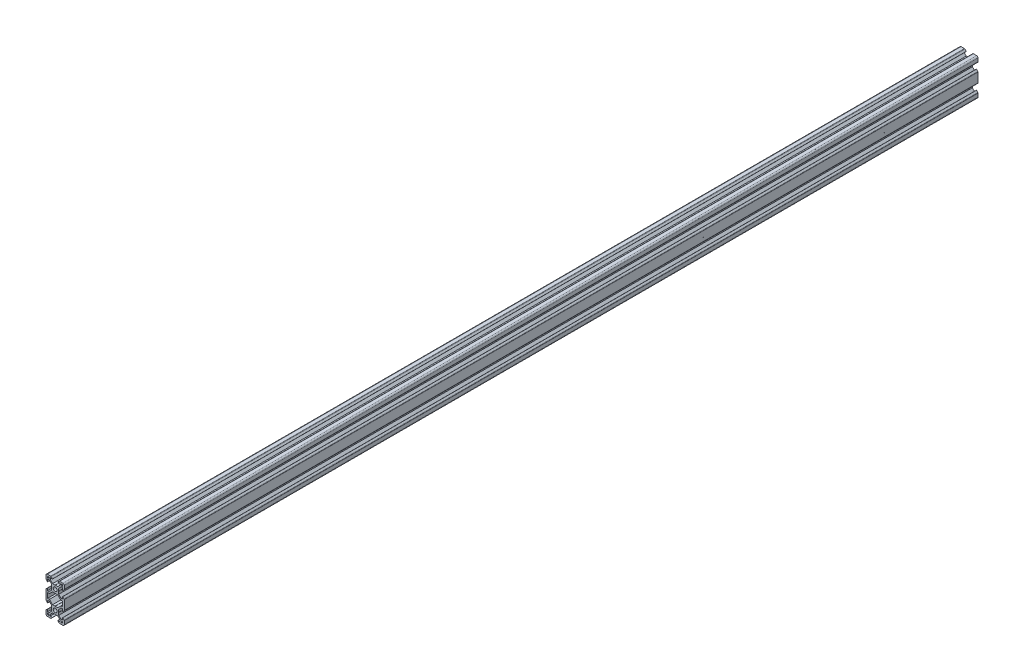
SolidWorks part; units mm, degrees
ref_plane "Front Plane" through (0, 0, 0) normal (0, 0, 1) x (1, 0, 0)
ref_plane "Top Plane" through (0, 0, 0) normal (0, 1, 0) x (1, 0, 0)
ref_plane "Right Plane" through (0, 0, 0) normal (1, 0, 0) x (0, 0, -1)
sketch "Sketch1" plane through (0, 0, 0) normal (0, 0, 1) x (1, 0, 0)
  line L0 (-8.2, 2.8875) -> (-8.2, 5.4975)
  line L3 (-4.9072, 9.9975) -> (-8.5, 9.9975)
  line L4 (-10, 4.9047) -> (-10, 8.4975)
  line L5 (-2.1, 0) -> (-3.8, 0) construction
  line L6 (0, 3.8) -> (0, 0) construction
  line L7 (-0.1, 3.9) -> (-2.8404, 3.9)
  line L8 (-3.9, 0.1) -> (-3.9, 2.8383)
  line L9 (-2.89, 8.1975) -> (-5.5, 8.1975)
  line L10 (-6.57, 8.1975) -> (-6.57, 7.6575)
  line L11 (-8.2, 6.5675) -> (-7.66, 6.5675)
  line L12 (-5.5, 8.1975) -> (-5.5, 6.5588)
  line L13 (-6.56, 5.4975) -> (-8.2, 5.4975)
  line L14 (-8.2, 8.1975) -> (-1.4852, 1.4847) construction
  line L15 (-6.56, 5.4975) -> (-3.9, 2.8383)
  line L16 (-5.5, 6.5588) -> (-2.8404, 3.9)
  line L17 (-7.66, 6.5675) -> (-6.57, 7.6575)
  line L18 (-8.7302, 7.6671) -> (-0.5302, -0.5304) construction
  line L19 (-7.6698, 8.7279) -> (0.5302, 0.5304) construction
  line L20 (-8.2, 8.1975) -> (0, 0) construction
  line L21 (-8.2, 6.5675) -> (-8.2, 8.1975)
  line L22 (-8.2, -0.0025) -> (-8.2, 8.1975) construction
  line L23 (-6.57, 8.1975) -> (-8.2, 8.1975)
  line L24 (0, 8.1975) -> (-8.2, 8.1975) construction
  line L25 (-10, -0.0025) -> (-10, 9.9975) construction
  line L26 (0, 9.9975) -> (-10, 9.9975) construction
  line L27 (-2.89, 8.3075) -> (-2.89, 8.1975)
  line L29 (-8.31, 2.8875) -> (-8.2, 2.8875)
  line L30 (-4.3486, 9.7661) -> (-2.89, 8.3075)
  line L31 (-8.31, 2.8875) -> (-9.7686, 4.3461)
  line L34 (-0.1, 3.9) -> (0, 3.8)
  line L35 (-3.9, 0.1) -> (-3.8, 0)
  line L36 (-8.2, -7.2996) -> (-6.24, -7.2996)
  line L37 (0, 0) -> (0, -10) construction
  line L38 (-0.1, -3.9) -> (-2.8404, -3.9)
  line L39 (-3.8, 0) -> (-3.9, -0.1)
  line L40 (-3.9, -0.1) -> (-3.9, -2.84)
  line L41 (-2.8404, -3.9) -> (-6.24, -7.2996)
  line L42 (-3.9, -2.84) -> (-6.56, -5.5)
  line L43 (-8.2, -2.89) -> (-8.2, -5.5)
  line L44 (-6.56, 5.4975) -> (-6.56, -5.5) construction
  line L45 (-6.56, -5.5) -> (-8.2, -5.5)
  line L46 (-0.1, -3.9) -> (0, -3.8)
  line L48 (-8.2, -2.89) -> (-8.31, -2.89)
  line L49 (-8.31, -2.89) -> (-9.7657, -4.3457)
  line L52 (-10, -10) -> (0, -10) construction
  line L53 (-8.2, -7.2996) -> (-8.2, -10)
  line L61 (-10, -4.9114) -> (-10, -10)
  arc A1 (-10, 8.4975) -> (-8.5, 9.9975) centre (-8.5, 8.4975) cw
  arc A2 (-9.7686, 4.3461) -> (-10, 4.9047) centre (-9.21, 4.9047) cw
  arc A3 (-4.3486, 9.7661) -> (-4.9072, 9.9975) centre (-4.9072, 9.2075) ccw
  arc A4 (-9.7657, -4.3457) -> (-10, -4.9114) centre (-9.2, -4.9114) ccw
  arc A6 (0, 2.1) -> (0, -2.1) centre (0, 0) ccw
  point P29 (-10, 9.9975)
  point P39 (-10, 4.5775)
  point P42 (-4.58, 9.9975)
  point P48 (-10, -4.58)
  dimension "D15" = 1.5
  dimension "D22" = 0.79
  dimension "D30" = 1.96
  dimension "D31" = 2.1
  dimension "D39" = 0.8
  dimension "D4" = 1.8
  dimension "D5" = 3.43
  dimension "D6" = 3.43
  dimension "D7" = 0.54
  dimension "D8" = 0.54
  dimension "D9" = 1.07
  dimension "D10" = 1.07
  dimension "D11" = 3.9
  dimension "D12" = 3.9
  dimension "D16" = 7.11
  dimension "D17" = 0.11
  dimension "D18" = 1.69
  dimension "D19" = 0.11
  dimension "D20" = 7.11
  dimension "D21" = 1.69
  dimension "D23" = 10
  dimension "D24" = 0.1
  dimension "D25" = 45
  dimension "D26" = 0.1
  dimension "D27" = 45
  dimension "D28" = 1.64
  dimension "D29" = 10
  dimension "D32" = 3.9
  dimension "D33" = 45
  dimension "D34" = 2.74
  dimension "D35" = 45
  dimension "D37" = 2.61
  dimension "D38" = 90
  dimension "D40" = 0.1
  dimension "D41" = 45
  dimension "D13" = 0.75
  dimension "D14" = 0.75
sketch "Sketch2" plane through (0, 0, 0) normal (0, 0, 1) x (1, 0, 0)
  line L0 (-0.1, 3.9) -> (0, 3.8) construction
  line L1 (-0.1, 3.9) -> (-2.8404, 3.9) construction
  line L2 (-5.5, 6.5588) -> (-2.8404, 3.9) construction
  line L3 (-5.5, 8.1975) -> (-5.5, 6.5588) construction
  line L4 (-2.89, 8.1975) -> (-5.5, 8.1975) construction
  line L5 (-7.66, 6.5675) -> (-6.57, 7.6575)
  line L6 (-6.57, 7.6575) -> (-6.57, 8.1975)
  line L7 (-6.57, 8.1975) -> (-8.2, 8.1975)
  line L8 (-8.2, 8.1975) -> (-8.2, 6.5675)
  line L9 (-8.2, 6.5675) -> (-7.66, 6.5675)
  line L10 (-7.66, 6.5675) -> (-6.57, 7.6575)
  line L11 (-6.57, 7.6575) -> (-6.57, 8.1975)
  line L12 (-6.57, 8.1975) -> (-8.2, 8.1975)
  line L13 (-8.2, 8.1975) -> (-8.2, 6.5675)
  line L14 (-8.2, 6.5675) -> (-7.66, 6.5675)
  line L15 (-2.89, 8.3075) -> (-2.89, 8.1975) construction
  line L16 (-4.3486, 9.7661) -> (-2.89, 8.3075) construction
  line L17 (-4.9072, 9.9975) -> (-8.5, 9.9975) construction
  line L18 (-10, 4.9047) -> (-10, 8.4975) construction
  line L19 (-8.31, 2.8875) -> (-9.7686, 4.3461) construction
  line L20 (-8.31, 2.8875) -> (-8.2, 2.8875) construction
  line L21 (-8.2, 2.8875) -> (-8.2, 5.4975) construction
  line L22 (-6.56, 5.4975) -> (-8.2, 5.4975) construction
  line L23 (-6.56, 5.4975) -> (-3.9, 2.8383) construction
  line L24 (-3.9, 0.1) -> (-3.9, 2.8383) construction
  line L25 (-3.9, 0.1) -> (-3.8, 0) construction
  line L26 (-3.8, 0) -> (-3.9, -0.1) construction
  line L27 (-3.9, -0.1) -> (-3.9, -2.84) construction
  line L28 (-3.9, -2.84) -> (-6.56, -5.5) construction
  line L29 (-6.56, -5.5) -> (-8.2, -5.5) construction
  line L30 (-8.2, -2.89) -> (-8.2, -5.5) construction
  line L31 (-8.2, -2.89) -> (-8.31, -2.89) construction
  line L32 (-8.31, -2.89) -> (-9.7657, -4.3457) construction
  line L33 (-10, -4.9114) -> (-10, -10) construction
  line L34 (-0.1, -3.9) -> (0, -3.8) construction
  line L35 (-0.1, -3.9) -> (-2.8404, -3.9) construction
  line L36 (-2.8404, -3.9) -> (-6.24, -7.2996) construction
  line L37 (-8.2, -7.2996) -> (-6.24, -7.2996) construction
  line L38 (-8.2, -7.2996) -> (-8.2, -10) construction
  line L39 (-0.1, 3.9) -> (0, 3.8)
  line L40 (-0.1, 3.9) -> (-2.8404, 3.9)
  line L41 (-5.5, 6.5588) -> (-2.8404, 3.9)
  line L42 (-5.5, 8.1975) -> (-5.5, 6.5588)
  line L43 (-2.89, 8.1975) -> (-5.5, 8.1975)
  line L44 (-2.89, 8.3075) -> (-2.89, 8.1975)
  line L45 (-4.3486, 9.7661) -> (-2.89, 8.3075)
  line L46 (-4.9072, 9.9975) -> (-8.5, 9.9975)
  line L47 (-10, 4.9047) -> (-10, 8.4975)
  line L48 (-8.31, 2.8875) -> (-9.7686, 4.3461)
  line L49 (-8.31, 2.8875) -> (-8.2, 2.8875)
  line L50 (-8.2, 2.8875) -> (-8.2, 5.4975)
  line L51 (-6.56, 5.4975) -> (-8.2, 5.4975)
  line L52 (-6.56, 5.4975) -> (-3.9, 2.8383)
  line L53 (-3.9, 0.1) -> (-3.9, 2.8383)
  line L54 (-3.9, 0.1) -> (-3.8, 0)
  line L55 (-3.8, 0) -> (-3.9, -0.1)
  line L56 (-3.9, -0.1) -> (-3.9, -2.84)
  line L57 (-3.9, -2.84) -> (-6.56, -5.5)
  line L58 (-6.56, -5.5) -> (-8.2, -5.5)
  line L59 (-8.2, -2.89) -> (-8.2, -5.5)
  line L60 (-8.2, -2.89) -> (-8.31, -2.89)
  line L61 (-8.31, -2.89) -> (-9.7657, -4.3457)
  line L62 (-10, -4.9114) -> (-10, -15.0886)
  line L63 (-0.1, -3.9) -> (0, -3.8)
  line L64 (-0.1, -3.9) -> (-2.8404, -3.9)
  line L65 (-2.8404, -3.9) -> (-6.24, -7.2996)
  line L66 (-8.2, -7.2996) -> (-6.24, -7.2996)
  line L67 (-8.2, -7.2996) -> (-8.2, -12.7004)
  line L68 (0, 0) -> (0, -10) construction
  line L69 (-10, -10) -> (0, -10) construction
  line L70 (0, 0) -> (0, -20) construction
  line L71 (-10, -10) -> (10, -10) construction
  line L72 (8.2, -7.2996) -> (8.2, -12.7004)
  line L73 (8.2, -7.2996) -> (6.24, -7.2996)
  line L74 (2.8404, -3.9) -> (6.24, -7.2996)
  line L75 (0.1, -3.9) -> (2.8404, -3.9)
  line L76 (0.1, -3.9) -> (0, -3.8)
  line L77 (10, -4.9114) -> (10, -15.0886)
  line L78 (8.31, -2.89) -> (9.7657, -4.3457)
  line L79 (8.2, -2.89) -> (8.31, -2.89)
  line L80 (8.2, -2.89) -> (8.2, -5.5)
  line L81 (6.56, -5.5) -> (8.2, -5.5)
  line L82 (3.9, -2.84) -> (6.56, -5.5)
  line L83 (3.9, -0.1) -> (3.9, -2.84)
  line L84 (3.8, 0) -> (3.9, -0.1)
  line L85 (3.9, 0.1) -> (3.8, 0)
  line L86 (3.9, 0.1) -> (3.9, 2.8383)
  line L87 (6.56, 5.4975) -> (3.9, 2.8383)
  line L88 (6.56, 5.4975) -> (8.2, 5.4975)
  line L89 (8.2, 2.8875) -> (8.2, 5.4975)
  line L90 (8.31, 2.8875) -> (8.2, 2.8875)
  line L91 (8.31, 2.8875) -> (9.7686, 4.3461)
  line L92 (10, 4.9047) -> (10, 8.4975)
  line L93 (4.9072, 9.9975) -> (8.5, 9.9975)
  line L94 (4.3486, 9.7661) -> (2.89, 8.3075)
  line L95 (2.89, 8.3075) -> (2.89, 8.1975)
  line L96 (2.89, 8.1975) -> (5.5, 8.1975)
  line L97 (5.5, 8.1975) -> (5.5, 6.5588)
  line L98 (5.5, 6.5588) -> (2.8404, 3.9)
  line L99 (0.1, 3.9) -> (2.8404, 3.9)
  line L100 (0.1, 3.9) -> (0, 3.8)
  line L101 (8.2, 6.5675) -> (7.66, 6.5675)
  line L102 (8.2, 8.1975) -> (8.2, 6.5675)
  line L103 (6.57, 8.1975) -> (8.2, 8.1975)
  line L104 (6.57, 7.6575) -> (6.57, 8.1975)
  line L105 (7.66, 6.5675) -> (6.57, 7.6575)
  line L106 (7.66, -26.5675) -> (6.57, -27.6575)
  line L107 (6.57, -27.6575) -> (6.57, -28.1975)
  line L108 (6.57, -28.1975) -> (8.2, -28.1975)
  line L109 (8.2, -28.1975) -> (8.2, -26.5675)
  line L110 (8.2, -26.5675) -> (7.66, -26.5675)
  line L111 (0.1, -23.9) -> (0, -23.8)
  line L112 (0.1, -23.9) -> (2.8404, -23.9)
  line L113 (5.5, -26.5588) -> (2.8404, -23.9)
  line L114 (5.5, -28.1975) -> (5.5, -26.5588)
  line L115 (2.89, -28.1975) -> (5.5, -28.1975)
  line L116 (2.89, -28.3075) -> (2.89, -28.1975)
  line L117 (4.3486, -29.7661) -> (2.89, -28.3075)
  line L118 (4.9072, -29.9975) -> (8.5, -29.9975)
  line L119 (10, -24.9047) -> (10, -28.4975)
  line L120 (8.31, -22.8875) -> (9.7686, -24.3461)
  line L121 (8.31, -22.8875) -> (8.2, -22.8875)
  line L122 (8.2, -22.8875) -> (8.2, -25.4975)
  line L123 (6.56, -25.4975) -> (8.2, -25.4975)
  line L124 (6.56, -25.4975) -> (3.9, -22.8383)
  line L125 (3.9, -20.1) -> (3.9, -22.8383)
  line L126 (3.9, -20.1) -> (3.8, -20)
  line L127 (3.8, -20) -> (3.9, -19.9)
  line L128 (3.9, -19.9) -> (3.9, -17.16)
  line L129 (3.9, -17.16) -> (6.56, -14.5)
  line L130 (6.56, -14.5) -> (8.2, -14.5)
  line L131 (8.2, -17.11) -> (8.2, -14.5)
  line L132 (8.2, -17.11) -> (8.31, -17.11)
  line L133 (8.31, -17.11) -> (9.7657, -15.6543)
  line L134 (0.1, -16.1) -> (0, -16.2)
  line L135 (0.1, -16.1) -> (2.8404, -16.1)
  line L136 (2.8404, -16.1) -> (6.24, -12.7004)
  line L137 (8.2, -12.7004) -> (6.24, -12.7004)
  line L138 (-8.2, -12.7004) -> (-6.24, -12.7004)
  line L139 (-2.8404, -16.1) -> (-6.24, -12.7004)
  line L140 (-0.1, -16.1) -> (-2.8404, -16.1)
  line L141 (-0.1, -16.1) -> (0, -16.2)
  line L142 (-8.31, -17.11) -> (-9.7657, -15.6543)
  line L143 (-8.2, -17.11) -> (-8.31, -17.11)
  line L144 (-8.2, -17.11) -> (-8.2, -14.5)
  line L145 (-6.56, -14.5) -> (-8.2, -14.5)
  line L146 (-3.9, -17.16) -> (-6.56, -14.5)
  line L147 (-3.9, -19.9) -> (-3.9, -17.16)
  line L148 (-3.8, -20) -> (-3.9, -19.9)
  line L149 (-3.9, -20.1) -> (-3.8, -20)
  line L150 (-3.9, -20.1) -> (-3.9, -22.8383)
  line L151 (-6.56, -25.4975) -> (-3.9, -22.8383)
  line L152 (-6.56, -25.4975) -> (-8.2, -25.4975)
  line L153 (-8.2, -22.8875) -> (-8.2, -25.4975)
  line L154 (-8.31, -22.8875) -> (-8.2, -22.8875)
  line L155 (-8.31, -22.8875) -> (-9.7686, -24.3461)
  line L156 (-10, -24.9047) -> (-10, -28.4975)
  line L157 (-4.9072, -29.9975) -> (-8.5, -29.9975)
  line L158 (-4.3486, -29.7661) -> (-2.89, -28.3075)
  line L159 (-2.89, -28.3075) -> (-2.89, -28.1975)
  line L160 (-2.89, -28.1975) -> (-5.5, -28.1975)
  line L161 (-5.5, -28.1975) -> (-5.5, -26.5588)
  line L162 (-5.5, -26.5588) -> (-2.8404, -23.9)
  line L163 (-0.1, -23.9) -> (-2.8404, -23.9)
  line L164 (-0.1, -23.9) -> (0, -23.8)
  line L165 (-8.2, -26.5675) -> (-7.66, -26.5675)
  line L166 (-8.2, -28.1975) -> (-8.2, -26.5675)
  line L167 (-6.57, -28.1975) -> (-8.2, -28.1975)
  line L168 (-6.57, -27.6575) -> (-6.57, -28.1975)
  line L169 (-7.66, -26.5675) -> (-6.57, -27.6575)
  arc A0 (0, 2.1) -> (0, -2.1) centre (0, 0) ccw construction
  arc A1 (-4.3486, 9.7661) -> (-4.9072, 9.9975) centre (-4.9072, 9.2075) ccw construction
  arc A2 (-8.5, 9.9975) -> (-10, 8.4975) centre (-8.5, 8.4975) ccw construction
  arc A3 (-10, 4.9047) -> (-9.7686, 4.3461) centre (-9.21, 4.9047) ccw construction
  arc A4 (-9.7657, -4.3457) -> (-10, -4.9114) centre (-9.2, -4.9114) ccw construction
  circle A5 centre (0, 0) radius 2.1
  arc A6 (-4.3486, 9.7661) -> (-4.9072, 9.9975) centre (-4.9072, 9.2075) ccw
  arc A7 (-8.5, 9.9975) -> (-10, 8.4975) centre (-8.5, 8.4975) ccw
  arc A8 (-10, 4.9047) -> (-9.7686, 4.3461) centre (-9.21, 4.9047) ccw
  arc A9 (-9.7657, -4.3457) -> (-10, -4.9114) centre (-9.2, -4.9114) ccw
  arc A10 (9.7657, -4.3457) -> (10, -4.9114) centre (9.2, -4.9114) cw
  arc A11 (10, 4.9047) -> (9.7686, 4.3461) centre (9.21, 4.9047) cw
  arc A12 (8.5, 9.9975) -> (10, 8.4975) centre (8.5, 8.4975) cw
  arc A13 (4.3486, 9.7661) -> (4.9072, 9.9975) centre (4.9072, 9.2075) cw
  arc A14 (4.3486, -29.7661) -> (4.9072, -29.9975) centre (4.9072, -29.2075) ccw
  arc A15 (8.5, -29.9975) -> (10, -28.4975) centre (8.5, -28.4975) ccw
  arc A16 (10, -24.9047) -> (9.7686, -24.3461) centre (9.21, -24.9047) ccw
  arc A17 (9.7657, -15.6543) -> (10, -15.0886) centre (9.2, -15.0886) ccw
  arc A18 (-9.7657, -15.6543) -> (-10, -15.0886) centre (-9.2, -15.0886) cw
  arc A19 (-10, -24.9047) -> (-9.7686, -24.3461) centre (-9.21, -24.9047) cw
  arc A20 (-8.5, -29.9975) -> (-10, -28.4975) centre (-8.5, -28.4975) cw
  arc A21 (-4.3486, -29.7661) -> (-4.9072, -29.9975) centre (-4.9072, -29.2075) cw
  circle A22 centre (0, -20) radius 2.1
  point P147 (8.2, -10)
  dimension "D1" = 0
extrude "Boss-Extrude1" add sketch "Sketch2" against normal blind 1000
